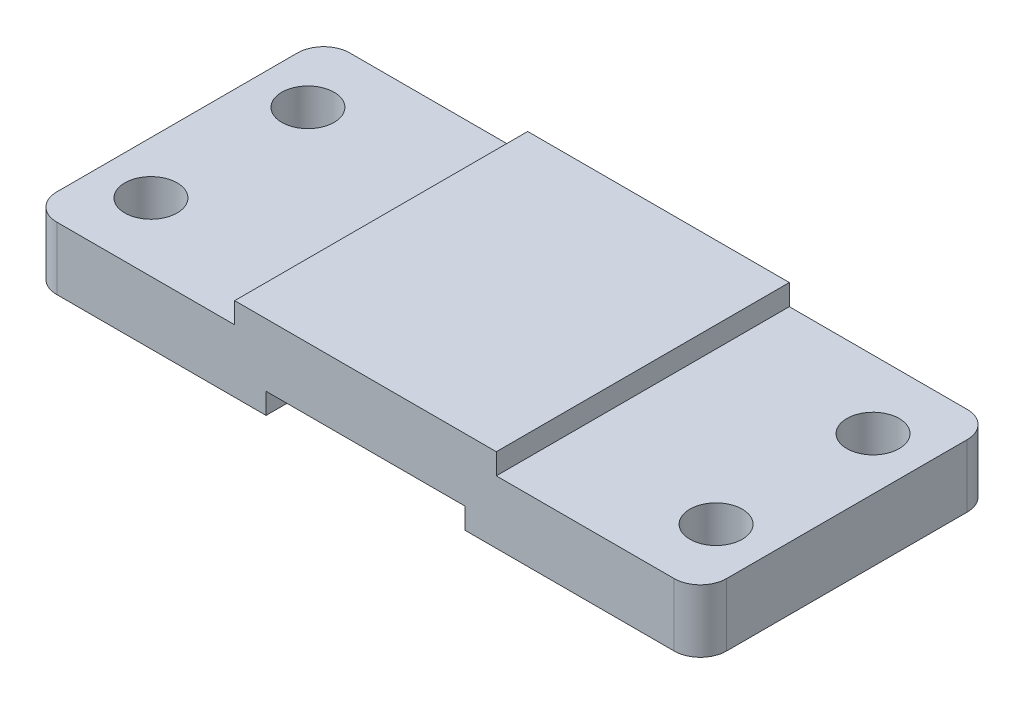
SolidWorks part; units mm, degrees
ref_plane "Ön Düzlem" through (0, 0, 0) normal (0, 0, 1) x (1, 0, 0)
ref_plane "Üst Düzlem" through (0, 0, 0) normal (0, 1, 0) x (1, 0, 0)
ref_plane "Sağ Düzlem" through (0, 0, 0) normal (1, 0, 0) x (0, 0, -1)
sketch "Çizim1" plane through (0, 0, 0) normal (0, 1, 0) x (1, 0, 0)
  line L1 (69.9975, 24.9032) -> (69.9975, -31.0968)
  line L4 (69.9975, -31.0968) -> (-58.0025, -31.0968)
  line L5 (-58.0025, 24.9032) -> (-58.0025, -31.0968)
  line L6 (-58.0025, 24.9032) -> (-19.0025, 24.9032)
  line L8 (-19.0025, 24.9032) -> (30.9975, 24.9032)
  line L9 (30.9975, 24.9032) -> (69.9975, 24.9032)
extrude "Yükseklik-Ekstrüzyon1" add sketch "Çizim1" along normal blind 12
sketch "Çizim2" plane through (0, 12, 0) normal (0, 1, 0) x (1, 0, 0)
  line L1 (69.9975, 24.9032) -> (-58.0025, 24.9032) construction
  line L2 (-19.0025, 24.9032) -> (30.9975, 24.9032)
  line L4 (-19.0025, 24.9032) -> (-19.0025, -31.0968)
  line L5 (-58.0025, -31.0968) -> (69.9975, -31.0968) construction
  line L6 (-19.0025, -31.0968) -> (30.9975, -31.0968)
  line L7 (30.9975, -31.0968) -> (30.9975, 24.9032)
extrude "Yükseklik-Ekstrüzyon2" add sketch "Çizim2" along normal blind 4
sketch "Çizim3" plane through (0, 0, 31.0968) normal (0, 0, 1) x (1, 0, 0)
  line L0 (24.9975, 0) -> (-13.0025, 0)
  line L1 (-58.0025, 0) -> (69.9975, 0) construction
  line L2 (-13.0025, 0) -> (-13.0025, 4)
  line L3 (24.9975, 0) -> (24.9975, 4)
  line L4 (-13.0025, 4) -> (24.9975, 4)
extrude "Kes-Ekstrüzyon1" cut sketch "Çizim3" against normal blind 56
sketch "Çizim4" plane through (0, 12, 0) normal (0, 1, 0) x (1, 0, 0)
  circle A0 centre (-48.0025, 11.9032) radius 5
  circle A1 centre (-48.0025, -18.0968) radius 5
  circle A2 centre (59.9975, -18.0968) radius 5
  circle A3 centre (59.9975, 11.9032) radius 5
extrude "Kes-Ekstrüzyon2" cut sketch "Çizim4" against normal blind 56
sketch "Çizim5" plane through (0, 12, 0) normal (0, 1, 0) x (1, 0, 0)
  line L0 (-19.0025, 24.9032) -> (-58.0025, 24.9032) construction
  line L1 (-58.0025, 24.9032) -> (-58.0025, -31.0968) construction
  line L2 (-58.0025, 19.9032) -> (-58.0025, 24.9032)
  line L3 (-58.0025, 24.9032) -> (-53.0025, 24.9032)
  line L4 (69.9975, -26.0968) -> (69.9975, -31.0968)
  line L5 (-58.0025, -31.0968) -> (-53.0025, -31.0968)
  line L6 (-58.0025, -26.0968) -> (-58.0025, -31.0968)
  line L9 (69.9975, -31.0968) -> (64.9975, -31.0968)
  line L10 (69.9975, 24.9032) -> (64.9975, 24.9032)
  line L11 (69.9975, 19.9032) -> (69.9975, 24.9032)
  arc A0 (-53.0025, 24.9032) -> (-58.0025, 19.9032) centre (-53.0025, 19.9032) ccw
  arc A1 (-53.0025, -31.0968) -> (-58.0025, -26.0968) centre (-53.0025, -26.0968) cw
  arc A2 (64.9975, -31.0968) -> (69.9975, -26.0968) centre (64.9975, -26.0968) ccw
  arc A3 (64.9975, 24.9032) -> (69.9975, 19.9032) centre (64.9975, 19.9032) cw
extrude "Kes-Ekstrüzyon3" cut sketch "Çizim5" against normal blind 56
